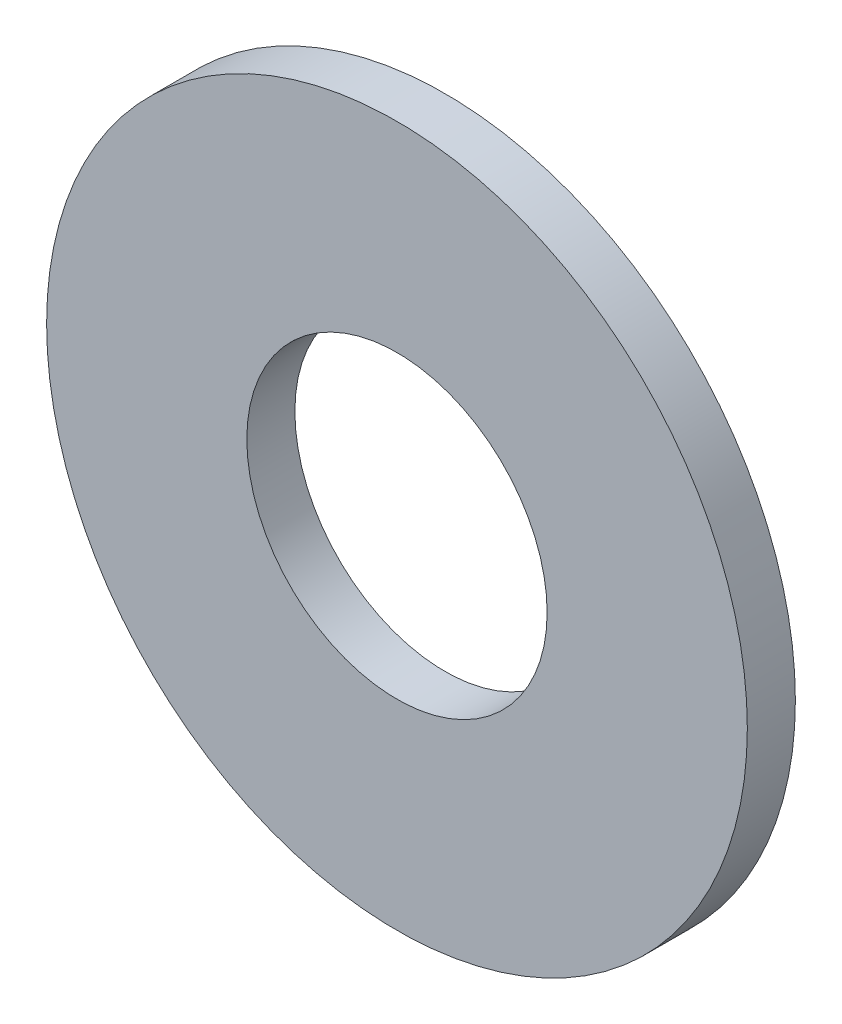
SolidWorks part; units mm, degrees
ref_plane "Front Plane" through (0, 0, 0) normal (0, 0, 1) x (1, 0, 0)
ref_plane "Top Plane" through (0, 0, 0) normal (0, 1, 0) x (1, 0, 0)
ref_plane "Right Plane" through (0, 0, 0) normal (1, 0, 0) x (0, 0, -1)
sketch "Sketch1" plane through (0, 0, 0) normal (0, 0, 1) x (1, 0, 0)
  circle A0 centre (0, 0) radius 2.3813
  circle A1 centre (0, 0) radius 5.5562
  dimension "ID" = 4.7625
  dimension "OD" = 11.1125
extrude "Extrude1" add sketch "Sketch1" against normal blind 0.762
